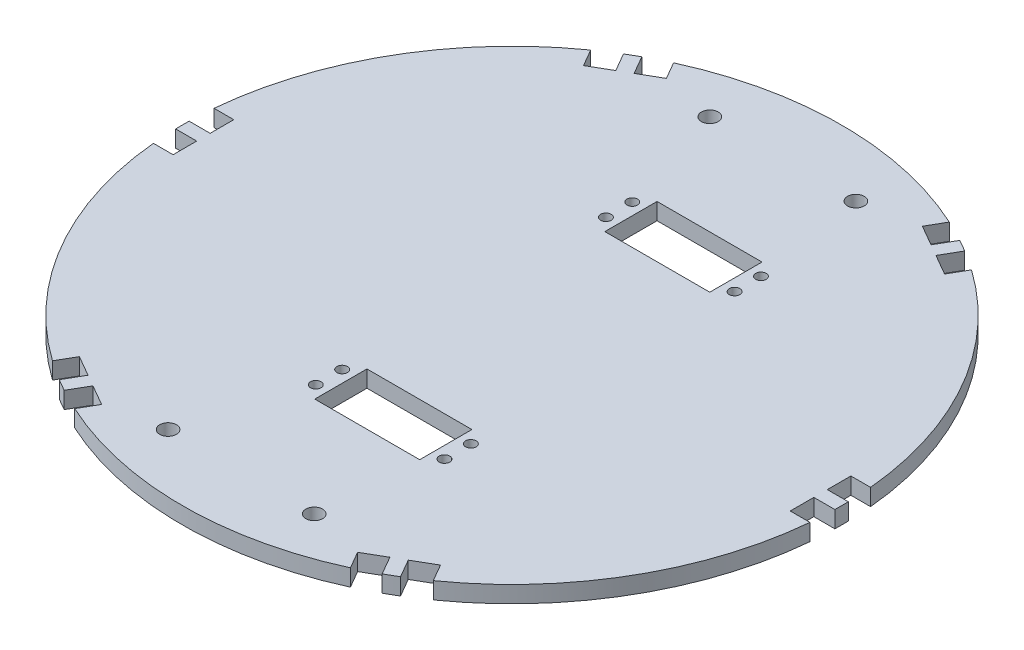
SolidWorks part; units mm, degrees
ref_plane "Front Plane" through (0, 0, 0) normal (0, 0, 1) x (1, 0, 0)
ref_plane "Top Plane" through (0, 0, 0) normal (0, 1, 0) x (1, 0, 0)
ref_plane "Right Plane" through (0, 0, 0) normal (1, 0, 0) x (0, 0, -1)
sketch "Sketch1" plane through (0, 0, 0) normal (0, 1, 0) x (1, 0, 0)
  line L0 (0, -125) -> (0, 125) construction
  line L1 (-125, 0) -> (125, 0) construction
  line L2 (-124.4699, 11.5) -> (-117, 11.5)
  line L3 (-117, 11.5) -> (-117, 2.55)
  line L4 (-117, 2.55) -> (-124.974, 2.55)
  line L5 (-52.2756, 113.5441) -> (-48.5407, 107.075)
  line L6 (-124.974, -2.55) -> (-117, -2.55)
  line L7 (-117, -2.55) -> (-117, -11.5)
  line L8 (-117, -11.5) -> (-124.4699, -11.5)
  line L9 (-48.5407, 107.075) -> (-56.2916, 102.6)
  line L10 (-56.2916, 102.6) -> (-60.2786, 109.5056)
  line L11 (-64.6954, 106.9556) -> (-60.7084, 100.05)
  line L12 (-60.7084, 100.05) -> (-68.4593, 95.575)
  line L13 (-68.4593, 95.575) -> (-72.1942, 102.0441)
  line L14 (72.1942, 102.0441) -> (68.4593, 95.575)
  line L15 (68.4593, 95.575) -> (60.7084, 100.05)
  line L16 (60.7084, 100.05) -> (64.6954, 106.9556)
  line L17 (60.2786, 109.5056) -> (56.2916, 102.6)
  line L18 (56.2916, 102.6) -> (48.5407, 107.075)
  line L19 (48.5407, 107.075) -> (52.2756, 113.5441)
  line L20 (124.4699, -11.5) -> (117, -11.5)
  line L21 (117, -11.5) -> (117, -2.55)
  line L22 (117, -2.55) -> (124.974, -2.55)
  line L23 (124.974, 2.55) -> (117, 2.55)
  line L24 (117, 2.55) -> (117, 11.5)
  line L25 (117, 11.5) -> (124.4699, 11.5)
  line L26 (0, 45.1) -> (0, 64.9) construction
  line L27 (-9.9, 64.9) -> (29.9, 64.9)
  line L28 (-9.9, 64.9) -> (-9.9, 45.1)
  line L29 (-9.9, 45.1) -> (29.9, 45.1)
  line L30 (29.9, 64.9) -> (29.9, 45.1)
  line L31 (-9.9, -45.1) -> (29.9, -45.1)
  line L32 (29.9, -64.9) -> (29.9, -45.1)
  line L33 (-9.9, -64.9) -> (29.9, -64.9)
  line L34 (-9.9, -64.9) -> (-9.9, -45.1)
  line L35 (29.9, 55) -> (34.4, 55) construction
  line L36 (34.4, 60) -> (34.4, 50) construction
  line L37 (10, 45.1) -> (10, 64.9) construction
  line L38 (52.2756, -113.5441) -> (48.5407, -107.075)
  line L39 (48.5407, -107.075) -> (56.2916, -102.6)
  line L40 (56.2916, -102.6) -> (60.2786, -109.5056)
  line L41 (64.6954, -106.9556) -> (60.7084, -100.05)
  line L42 (60.7084, -100.05) -> (68.4593, -95.575)
  line L43 (68.4593, -95.575) -> (72.1942, -102.0441)
  line L44 (-72.1942, -102.0441) -> (-68.4593, -95.575)
  line L45 (-68.4593, -95.575) -> (-60.7084, -100.05)
  line L46 (-60.7084, -100.05) -> (-64.6954, -106.9556)
  line L47 (-60.2786, -109.5056) -> (-56.2916, -102.6)
  line L48 (-56.2916, -102.6) -> (-48.5407, -107.075)
  line L49 (-48.5407, -107.075) -> (-52.2756, -113.5441)
  arc A0 (-124.974, 2.55) -> (-124.974, -2.55) centre (0, 0) ccw
  arc A1 (-124.4699, -11.5) -> (-72.1942, -102.0441) centre (0, 0) ccw
  arc A2 (-72.1942, 102.0441) -> (-124.4699, 11.5) centre (0, 0) ccw
  arc A3 (-60.2786, 109.5056) -> (-64.6954, 106.9556) centre (0, 0) ccw
  arc A4 (52.2756, 113.5441) -> (-52.2756, 113.5441) centre (0, 0) ccw
  arc A5 (64.6954, 106.9556) -> (60.2786, 109.5056) centre (0, 0) ccw
  arc A6 (124.4699, 11.5) -> (72.1942, 102.0441) centre (0, 0) ccw
  arc A7 (124.974, -2.55) -> (124.974, 2.55) centre (0, 0) ccw
  circle A13 centre (34.4, 60) radius 2
  circle A14 centre (34.4, 50) radius 2
  circle A15 centre (-14.4, 60) radius 2
  circle A16 centre (-14.4, 50) radius 2
  circle A17 centre (-14.4, -60) radius 2
  circle A18 centre (-14.4, -50) radius 2
  circle A19 centre (34.4, -60) radius 2
  circle A20 centre (34.4, -50) radius 2
  arc A21 (60.2786, -109.5056) -> (64.6954, -106.9556) centre (0, 0) ccw
  arc A22 (72.1942, -102.0441) -> (124.4699, -11.5) centre (0, 0) ccw
  arc A23 (-52.2756, -113.5441) -> (52.2756, -113.5441) centre (0, 0) ccw
  arc A24 (-64.6954, -106.9556) -> (-60.2786, -109.5056) centre (0, 0) ccw
  point P41 (0, 0)
  point P43 (-9.9, 55)
  point P55 (34.4, 55)
  dimension "D1" = 250
  dimension "D10" = 4
  dimension "D3" = 23
  dimension "D4" = 8
  dimension "D2" = 5.1
  dimension "D6" = 19.8
  dimension "D7" = 39.8
  dimension "D8" = 9.9
  dimension "D9" = 55
  dimension "D11" = 4.5
  dimension "D12" = 10
  dimension "D5" = 6
extrude "Boss-Extrude1" add sketch "Sketch1" along normal blind 6.35
sketch "Sketch3" plane through (0, 6.35, 0) normal (0, 1, 0) x (1, 0, 0)
  line L0 (0, 0) -> (62.829, 0) construction
  circle A0 centre (27.7, -102.7) radius 2.6035 construction
  circle A1 centre (-27.7, -102.7) radius 2.6035 construction
  circle A2 centre (27.7, -102.7) radius 2.6035 construction
  circle A3 centre (-27.7, -102.7) radius 2.6035 construction
  circle A4 centre (-27.7, -102.7) radius 3.175
  circle A5 centre (27.7, -102.7) radius 3.175
  circle A6 centre (27.7, 102.7) radius 3.175
  circle A7 centre (-27.7, 102.7) radius 3.175
  dimension "D1" = 6.35
extrude "Cut-Extrude1" cut sketch "Sketch3" against normal blind 6.35
equation "\"dg\"= 55"
equation "\"ds\"= 55"
equation "\"D9@Sketch1\"=(\"ds\"+\"dg\")/2"
